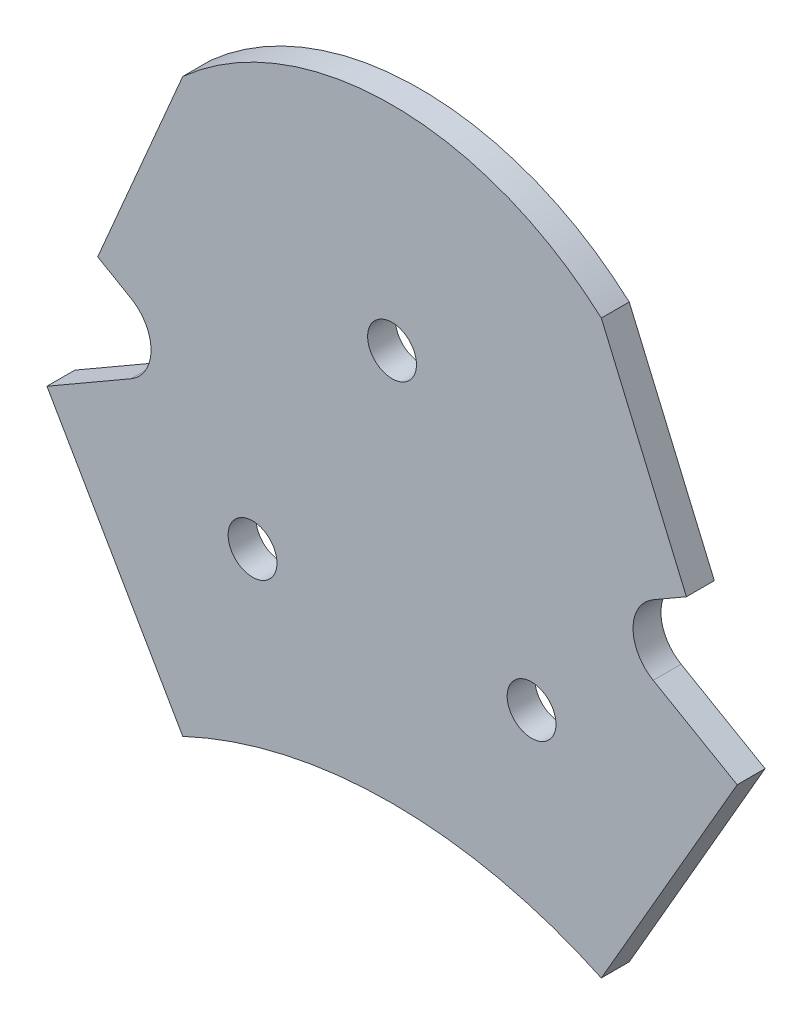
SolidWorks part; units mm, degrees
ref_plane "Front Plane" through (0, 0, 0) normal (0, 0, 1) x (1, 0, 0)
ref_plane "Top Plane" through (0, 0, 0) normal (0, 1, 0) x (1, 0, 0)
ref_plane "Right Plane" through (0, 0, 0) normal (1, 0, 0) x (0, 0, -1)
sketch "Sketch1" plane through (0, 0, 0) normal (0, 0, 1) x (1, 0, 0)
  line L0 (0, 23.094) -> (-20, -11.547) construction
  line L1 (-20, -11.547) -> (20, -11.547) construction
  line L2 (20, -11.547) -> (0, 23.094) construction
  line L3 (-20, -11.547) -> (0, 0) construction
  line L4 (0, 0) -> (20, -11.547) construction
  line L5 (0, 23.094) -> (0, 0) construction
  line L10 (0, -103.6202) -> (0, 0) construction
  line L11 (-30, -39.806) -> (30, -39.806) construction
  line L12 (-30, -39.806) -> (-49.473, -6.0778)
  line L13 (30, -39.806) -> (49.473, -6.0778)
  line L14 (0, -33.106) -> (-20, -33.106) construction
  line L15 (0, 19.594) -> (-20, 19.594) construction
  line L16 (20, -11.547) -> (39.7365, -22.9419) construction
  line L17 (-20, -11.547) -> (-39.7365, -22.9419) construction
  line L18 (-49.473, -6.0778) -> (-37.4352, 0.8722)
  line L19 (49.473, -6.0778) -> (37.4352, 0.8722)
  line L20 (-37.4352, 0.8722) -> (-37.4352, 10.8722) construction
  line L21 (-37.4352, 10.8722) -> (-42.1984, 13.6222)
  line L22 (-42.1984, 13.6222) -> (-30, 42.1213)
  line L23 (37.4352, 0.8722) -> (37.4352, 10.8722) construction
  line L24 (37.4352, 10.8722) -> (42.1984, 13.6222)
  line L25 (42.1984, 13.6222) -> (30, 42.1213)
  line L26 (0, 0) -> (0, 84.2427) construction
  line L28 (-37.4352, 0.8722) -> (37.4352, 0.8722) construction
  line L29 (-30, 42.1213) -> (-30, -39.806) construction
  line L30 (-42.1984, 13.6222) -> (42.1984, 13.6222) construction
  line L31 (-30, 42.1213) -> (30, 42.1213) construction
  line L32 (-30, 53.594) -> (30, 53.594) construction
  circle A0 centre (0, 23.094) radius 3.5
  circle A1 centre (-20, -11.547) radius 3.5
  circle A2 centre (20, -11.547) radius 3.5
  arc A3 (-30, -39.806) -> (30, -39.806) centre (0, -103.6202) cw
  arc A4 (-37.4352, 0.8722) -> (-37.4352, 10.8722) centre (-40.322, 5.8722) ccw
  arc A5 (37.4352, 0.8722) -> (37.4352, 10.8722) centre (40.322, 5.8722) cw
  arc A6 (-30, 42.1213) -> (30, 42.1213) centre (0, 8.634) cw
  point P28 (0, 53.594)
  point P29 (-30, 53.594)
  point P30 (0, 42.1213)
  dimension "D2" = 7
  dimension "D7" = 52.7
  dimension "D5" = 13.9
  dimension "D1" = 40
  dimension "D3" = 60
  dimension "D4" = 59.4
  dimension "D6" = 10
  dimension "D8" = 5.5
  dimension "D9" = 31
  dimension "D10" = 20
  dimension "D11" = 34
extrude "Boss-Extrude1" add sketch "Sketch1" along normal blind 4 contours A0 | A1 | A2 | L22 A6 L25 L24 A5 L19 L13 A3 L12 L18 A4 L21
